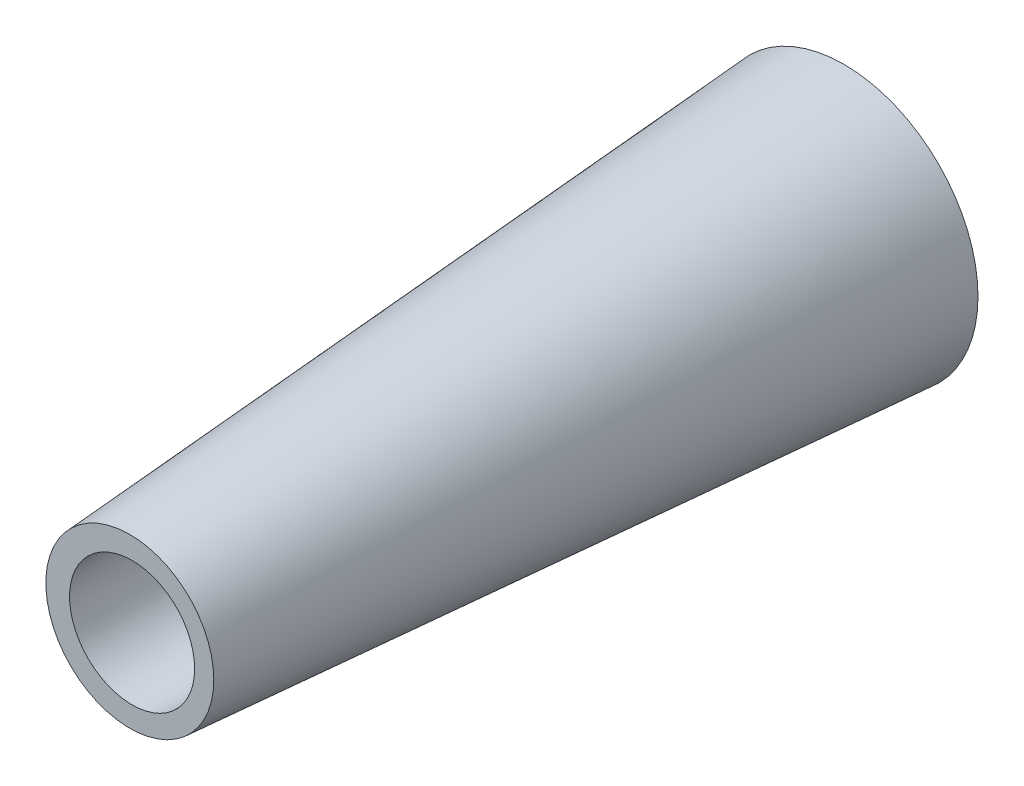
SolidWorks part; units mm, degrees
ref_plane "Ebene vorne" through (0, 0, 0) normal (0, 0, 1) x (1, 0, 0)
ref_plane "Ebene oben" through (0, 0, 0) normal (0, 1, 0) x (1, 0, 0)
ref_plane "Ebene rechts" through (0, 0, 0) normal (1, 0, 0) x (0, 0, -1)
sketch "Skizze1" plane through (0, 0, 0) normal (0, 0, 1) x (1, 0, 0)
  circle A0 centre (0, 0) radius 7.5
extrude "Aufsatz-Linear austragen2" add sketch "Skizze1" along normal blind 40 draft 4
sketch "Skizze3" plane through (0, 0, 40) normal (0, 0, 1) x (1, 0, 0)
  line L0 (0, 4.7029) -> (0, 3.5029)
  circle A0 centre (0, 0) radius 4.7029 construction
  circle A1 centre (0.1267, 0.0025) radius 3.5028
extrude "Schnitt-Linear austragen1" cut sketch "Skizze3" against normal blind 35 contours A1
